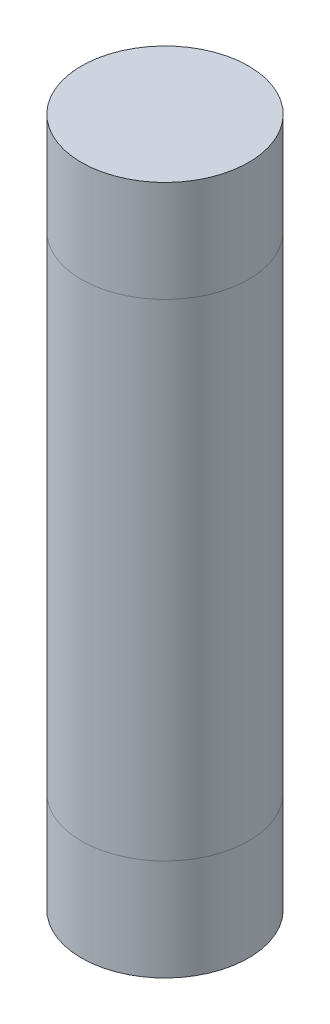
SolidWorks part; units mm, degrees
ref_plane "Front Plane" through (0, 0, 0) normal (0, 0, 1) x (1, 0, 0)
ref_plane "Top Plane" through (0, 0, 0) normal (0, 1, 0) x (1, 0, 0)
ref_plane "Right Plane" through (0, 0, 0) normal (1, 0, 0) x (0, 0, -1)
sketch "Sketch1" plane through (0, 0, 0) normal (0, 1, 0) x (1, 0, 0)
  circle A0 centre (0, 0) radius 8.25
  dimension "D1" = 16.5
extrude "Boss-Extrude1" add sketch "Sketch1" along normal blind 10
sketch "Sketch2" plane through (0, 10, 0) normal (0, 1, 0) x (1, 0, 0)
  circle A1 centre (0, 0) radius 8.25
  circle A2 centre (0, 0) radius 8.25
  dimension "D1" = 0
extrude "Boss-Extrude2" add sketch "Sketch2" along normal blind 48 separate body
sketch "Sketch3" plane through (0, 58, 0) normal (0, 1, 0) x (1, 0, 0)
  circle A1 centre (0, 0) radius 8.25
  circle A2 centre (0, 0) radius 8.25
  dimension "D1" = 0
extrude "Boss-Extrude3" add sketch "Sketch3" along normal blind 10 separate body
